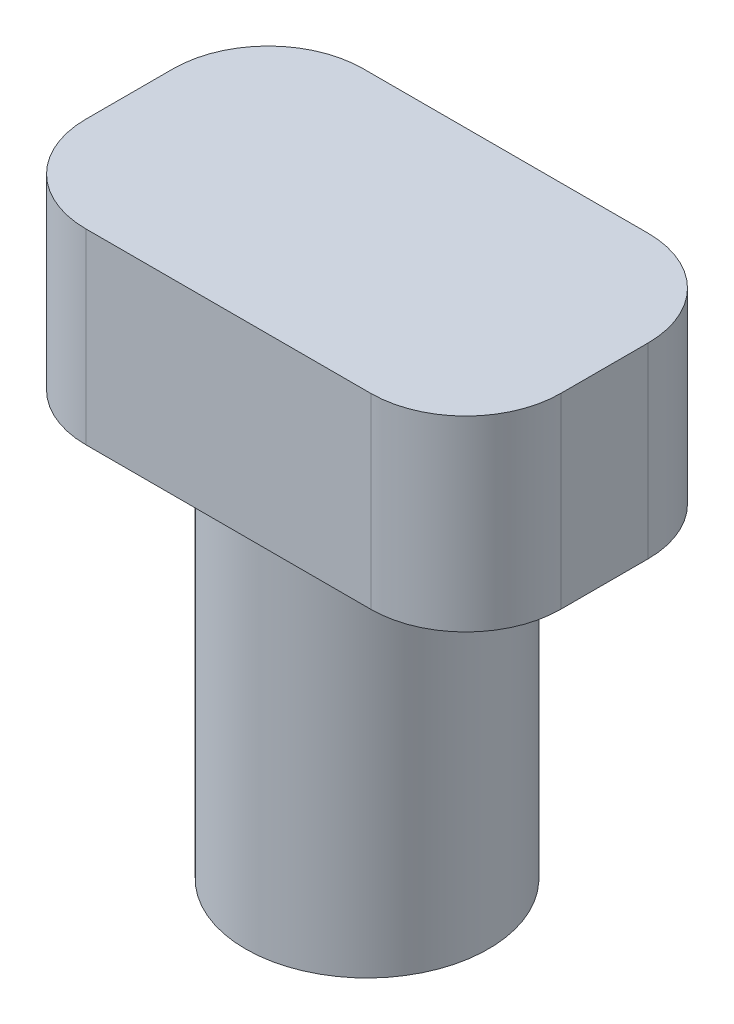
SolidWorks part; units mm, degrees
ref_plane "Front Plane" through (0, 0, 0) normal (0, 0, 1) x (1, 0, 0)
ref_plane "Top Plane" through (0, 0, 0) normal (0, 1, 0) x (1, 0, 0)
ref_plane "Right Plane" through (0, 0, 0) normal (1, 0, 0) x (0, 0, -1)
sketch "Sketch1" plane through (0, 0, 0) normal (0, 1, 0) x (1, 0, 0)
  circle A0 centre (0, 0) radius 3.25
  dimension "D1" = 6.5
extrude "Boss-Extrude1" add sketch "Sketch1" along normal blind 10 contours A0
sketch "Sketch2" plane through (0, 0, 0) normal (0, -1, 0) x (1, 0, 0)
  circle A1 centre (0, 0) radius 1.75
  dimension "D1" = 3.5
extrude "Cut-Extrude1" cut sketch "Sketch2" against normal blind 2.5
sketch "Sketch3" plane through (0, 10, 0) normal (0, 1, 0) x (1, 0, 0)
  line L1 (-6.35, 3.7084) -> (6.35, 3.7084)
  line L2 (-6.35, 3.7084) -> (-6.35, -3.7084)
  line L3 (-6.35, -3.7084) -> (6.35, -3.7084)
  line L4 (6.35, 3.7084) -> (6.35, -3.7084)
  line L5 (-6.35, 3.7084) -> (6.35, -3.7084) construction
  line L6 (-6.35, -3.7084) -> (6.35, 3.7084) construction
  point P0 (0, 0)
  dimension "D1" = 12.7
  dimension "D2" = 7.4168
extrude "Boss-Extrude2" add sketch "Sketch3" along normal blind 5
fillet "Fillet1" radius 2.54 4 edges at (-6.35, 12.5, -3.7084) (6.35, 12.5, -3.7084) (6.35, 12.5, 3.7084) (-6.35, 12.5, 3.7084)
